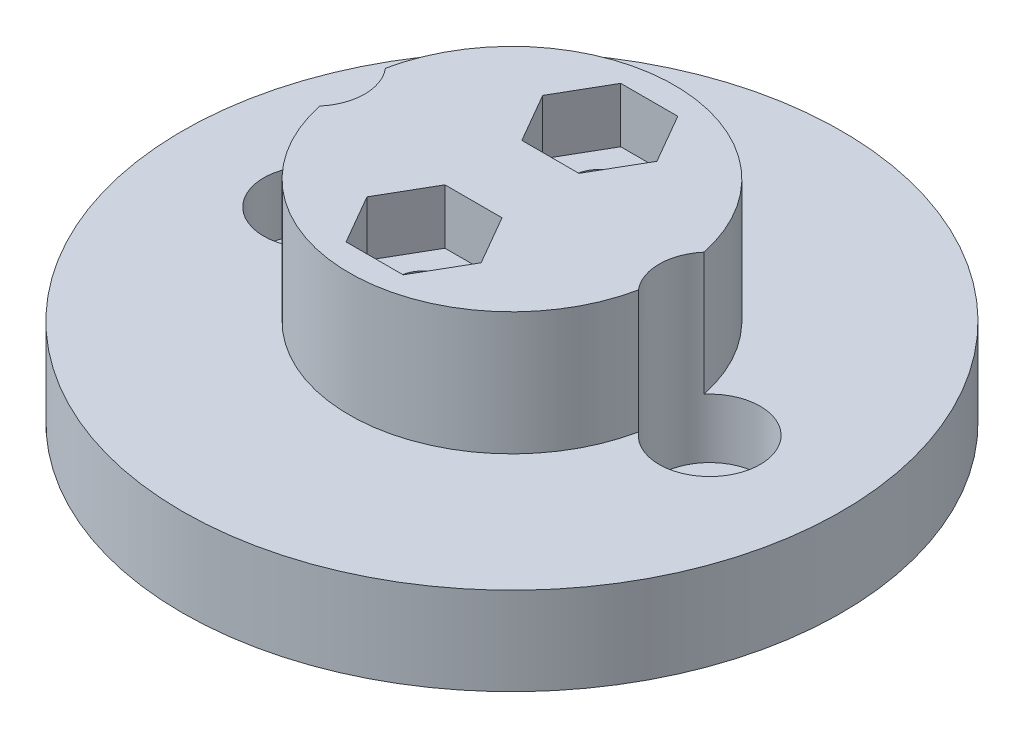
SolidWorks part; units mm, degrees
ref_plane "Front Plane" through (0, 0, 0) normal (0, 0, 1) x (1, 0, 0)
ref_plane "Top Plane" through (0, 0, 0) normal (0, 1, 0) x (1, 0, 0)
ref_plane "Right Plane" through (0, 0, 0) normal (1, 0, 0) x (0, 0, -1)
sketch "Sketch1" plane through (0, 0, 0) normal (0, 1, 0) x (1, 0, 0)
  circle A0 centre (0, 0) radius 19.05
  dimension "D1" = 38.1
extrude "Boss-Extrude1" add sketch "Sketch1" along normal blind 5.08
sketch "Sketch4" plane through (0, 5.08, 0) normal (0, 1, 0) x (1, 0, 0)
  circle A0 centre (0, 0) radius 9.398
  dimension "D1" = 18.796
extrude "Boss-Extrude2" add sketch "Sketch4" along normal blind 7.112
sketch "Sketch5" plane through (0, 5.08, 0) normal (0, 1, 0) x (1, 0, 0)
  circle A0 centre (-11.43, 0) radius 2.921
  circle A1 centre (11.43, 0) radius 2.921
  dimension "D1" = 5.842
  dimension "D2" = 5.842
  dimension "D3" = 22.86
  dimension "D4" = 11.43
extrude "Cut-Extrude1" cut sketch "Sketch5" against normal blind 3.429 and the other way through all
sketch "Sketch6" plane through (0, 5.08, 0) normal (0, 1, 0) x (1, 0, 0)
  circle A0 centre (-11.43, 0) radius 1.4605
  circle A1 centre (11.43, 0) radius 1.7371
  dimension "D1" = 2.921
extrude "Cut-Extrude2" cut sketch "Sketch6" against normal through all both
sketch "Sketch7" plane through (0, 12.192, 0) normal (0, 1, 0) x (1, 0, 0)
  line L1 (4.766, 0) -> (2.383, 4.1275)
  line L2 (2.383, 4.1275) -> (-2.383, 4.1275)
  line L3 (-2.383, 4.1275) -> (-4.766, 0)
  line L4 (-4.766, 0) -> (-2.383, -4.1275)
  line L5 (-2.383, -4.1275) -> (2.383, -4.1275)
  line L6 (2.383, -4.1275) -> (4.766, 0)
  circle A0 centre (0, 0) radius 4.1275 construction
  dimension "D1" = 8.255
extrude "Cut-Extrude3" [suppressed] cut sketch "Sketch7" against normal blind 3.81
sketch "Sketch8" plane through (0, 12.192, 0) normal (0, 1, 0) x (1, 0, 0)
  circle A0 centre (0, 0) radius 1.5875
extrude "Cut-Extrude4" [suppressed] cut sketch "Sketch8" against normal blind 7.62
sketch "Sketch9" plane through (0, 12.192, 0) normal (0, 1, 0) x (1, 0, 0)
  line L1 (3.2996, 5.08) -> (1.6498, 7.9375)
  line L2 (1.6498, 7.9375) -> (-1.6498, 7.9375)
  line L3 (-1.6498, 7.9375) -> (-3.2996, 5.08)
  line L4 (-3.2996, 5.08) -> (-1.6498, 2.2225)
  line L5 (-1.6498, 2.2225) -> (1.6498, 2.2225)
  line L6 (1.6498, 2.2225) -> (3.2996, 5.08)
  line L7 (3.2996, -5.08) -> (1.6498, -2.2225)
  line L8 (1.6498, -2.2225) -> (-1.6498, -2.2225)
  line L9 (-1.6498, -2.2225) -> (-3.2996, -5.08)
  line L10 (-3.2996, -5.08) -> (-1.6498, -7.9375)
  line L11 (-1.6498, -7.9375) -> (1.6498, -7.9375)
  line L12 (1.6498, -7.9375) -> (3.2996, -5.08)
  circle A0 centre (0, 5.08) radius 2.8575 construction
  circle A1 centre (0, -5.08) radius 2.8575 construction
  dimension "D1" = 5.715
  dimension "D2" = 5.715
  dimension "D3" = 10.16
  dimension "D4" = 5.08
extrude "Cut-Extrude5" cut sketch "Sketch9" against normal blind 3.175
sketch "Sketch10" plane through (0, 12.192, 0) normal (0, 1, 0) x (1, 0, 0)
  circle A0 centre (0, 5.08) radius 1.5875
  circle A1 centre (0, -5.08) radius 1.5875
  point P4 (0, 0)
  point P6 (0, 0)
  point P7 (0, 0)
  dimension "D1" = 3.175
  dimension "D2" = 3.175
  dimension "D3" = 5.08
  dimension "D4" = 10.16
extrude "Cut-Extrude6" cut sketch "Sketch10" against normal blind 7.62
